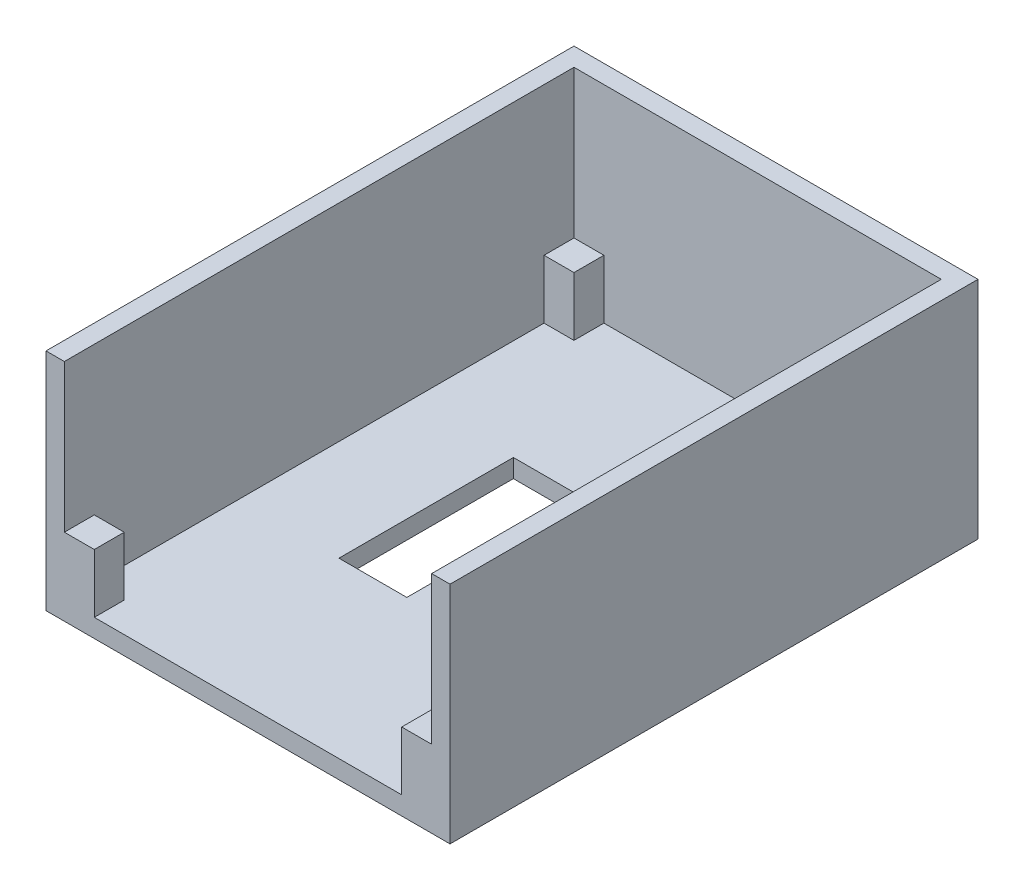
SolidWorks part; units mm, degrees
ref_plane "Front Plane" through (0, 0, 0) normal (0, 0, 1) x (1, 0, 0)
ref_plane "Top Plane" through (0, 0, 0) normal (0, 1, 0) x (1, 0, 0)
ref_plane "Right Plane" through (0, 0, 0) normal (1, 0, 0) x (0, 0, -1)
sketch "Sketch1" plane through (0, 0, 0) normal (0, 1, 0) x (1, 0, 0)
  line L1 (25.4, -35.2425) -> (-25.4, -35.2425)
  line L2 (25.4, -35.2425) -> (25.4, 35.2425)
  line L3 (25.4, 35.2425) -> (-25.4, 35.2425)
  line L4 (-25.4, -35.2425) -> (-25.4, 35.2425)
  line L5 (25.4, -35.2425) -> (-25.4, 35.2425) construction
  line L6 (25.4, 35.2425) -> (-25.4, -35.2425) construction
  point P0 (0, 0)
  dimension "D1" = 50.8
  dimension "D2" = 70.485
extrude "Boss-Extrude1" add sketch "Sketch1" along normal blind 2.54
sketch "Sketch5" plane through (0, 0, 0) normal (0, 1, 0) x (1, 0, 0)
  line L0 (25.4, -35.2425) -> (25.4, 35.2425) construction
  line L2 (27.94, -35.2425) -> (27.94, 37.7825)
  line L3 (27.94, 37.7825) -> (-27.94, 37.7825)
  line L4 (-27.94, -35.2425) -> (-27.94, 37.7825)
  line L5 (27.94, -35.2425) -> (-27.94, 37.7825) construction
  line L6 (27.94, 37.7825) -> (-27.94, -35.2425) construction
  line L8 (25.4, -35.2425) -> (25.4, 35.2425)
  line L9 (25.4, 35.2425) -> (-25.4, 35.2425)
  line L10 (-25.4, -35.2425) -> (-25.4, 35.2425)
  line L11 (25.4, -35.2425) -> (-25.4, 35.2425) construction
  line L12 (25.4, 35.2425) -> (-25.4, -35.2425) construction
  line L13 (-25.4, -35.2425) -> (25.4, -35.2425) construction
  line L14 (-27.94, -35.2425) -> (-25.4, -35.2425)
  line L15 (25.4, -35.2425) -> (27.94, -35.2425)
  point P0 (0, 0)
  point P6 (0, 0)
  dimension "D1" = 2.54
  dimension "D2" = 2.54
  dimension "D3" = 2.54
extrude "Boss-Extrude2" add sketch "Sketch5" along normal blind 31.115
sketch "Sketch6" plane through (0, 2.54, 0) normal (0, 1, 0) x (1, 0, 0)
  line L1 (-25.4, 35.2425) -> (-21.2598, 35.2425)
  line L2 (-25.4, 35.2425) -> (-25.4, 31.1023)
  line L3 (-25.4, 31.1023) -> (-21.2598, 31.1023)
  line L4 (-21.2598, 35.2425) -> (-21.2598, 31.1023)
  line L5 (25.4, 35.2425) -> (21.2598, 35.2425)
  line L6 (25.4, 35.2425) -> (25.4, 31.1023)
  line L7 (25.4, 31.1023) -> (21.2598, 31.1023)
  line L8 (21.2598, 35.2425) -> (21.2598, 31.1023)
  line L9 (25.4, -35.2425) -> (21.2598, -35.2425)
  line L10 (25.4, -35.2425) -> (25.4, -31.1023)
  line L11 (25.4, -31.1023) -> (21.2598, -31.1023)
  line L12 (21.2598, -35.2425) -> (21.2598, -31.1023)
  line L13 (-25.4, -35.2425) -> (-21.2598, -35.2425)
  line L14 (-25.4, -35.2425) -> (-25.4, -31.1023)
  line L15 (-25.4, -31.1023) -> (-21.2598, -31.1023)
  line L16 (-21.2598, -35.2425) -> (-21.2598, -31.1023)
  dimension "D1" = 4.1402
extrude "Boss-Extrude3" add sketch "Sketch6" along normal blind 8.128
sketch "Sketch8" plane through (0, 2.54, 0) normal (0, 1, 0) x (1, 0, 0)
  line L0 (-25.4, 31.1023) -> (-25.4, -31.1023) construction
  line L1 (-11.43, 12.8905) -> (-2.032, 12.8905)
  line L2 (-11.43, 12.8905) -> (-11.43, -11.2395)
  line L3 (-11.43, -11.2395) -> (-2.032, -11.2395)
  line L4 (-2.032, 12.8905) -> (-2.032, -11.2395)
  line L5 (-25.4, 35.2425) -> (25.4, 35.2425) construction
  dimension "D1" = 13.97
  dimension "D2" = 22.352
  dimension "D3" = 9.398
  dimension "D4" = 24.13
extrude "Cut-Extrude2" cut sketch "Sketch8" against normal through all
